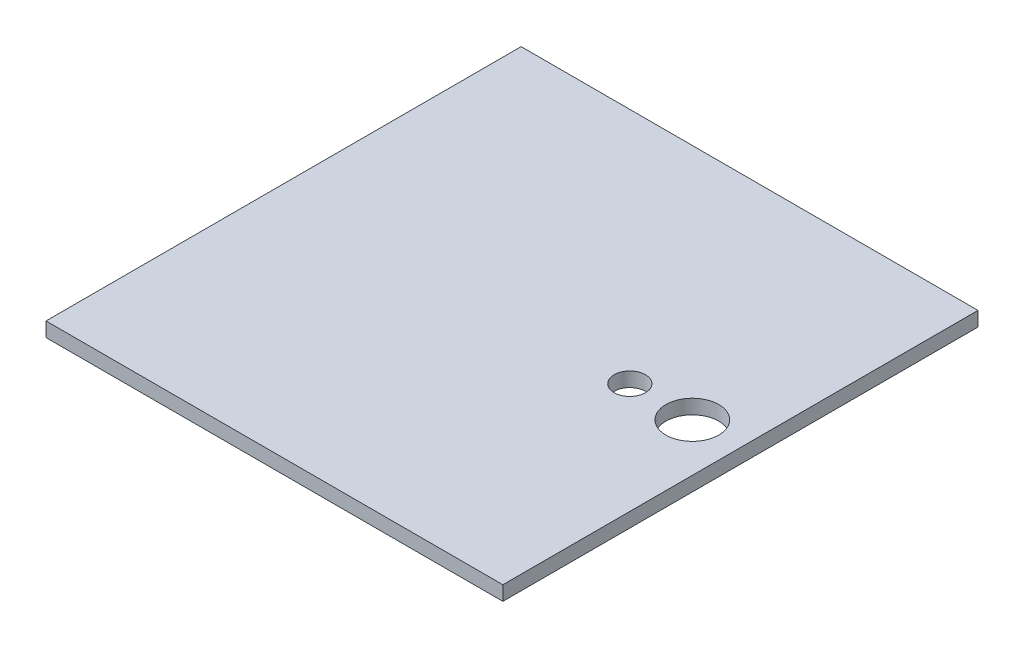
SolidWorks part; units mm, degrees
ref_plane "Front Plane" through (0, 0, 0) normal (0, 0, 1) x (1, 0, 0)
ref_plane "Top Plane" through (0, 0, 0) normal (0, 1, 0) x (1, 0, 0)
ref_plane "Right Plane" through (0, 0, 0) normal (1, 0, 0) x (0, 0, -1)
sketch "Sketch1" plane through (0, 0, 0) normal (0, 1, 0) x (1, 0, 0)
  line L1 (-101.2815, 20.698) -> (-6.2815, 20.698)
  line L2 (-101.2815, 20.698) -> (-101.2815, -78.102)
  line L3 (-101.2815, -78.102) -> (-6.2815, -78.102)
  line L4 (-6.2815, 20.698) -> (-6.2815, -78.102)
  circle A0 centre (-16.2815, -28.702) radius 5.5
  circle A1 centre (-29.2815, -28.702) radius 3.25
  point P8 (0, 0)
  dimension "D3" = 11
  dimension "D4" = 6.5
  dimension "D1" = 95
  dimension "D2" = 98.8
  dimension "D5" = 49.4
  dimension "D6" = 10
  dimension "D7" = 23
extrude "Boss-Extrude1" add sketch "Sketch1" along normal blind 3
equation "\"Fit\"= 1"
equation "\"cover width\"= 98.8"
equation "\"top 1 length\"= 95"
equation "\"thinner acrylic\"= 3"
equation "\"D1@Sketch1\"=\"top 1 length\""
equation "\"D2@Sketch1\"=\"cover width\""
equation "\"D1@Boss-Extrude1\"=\"thinner acrylic\""
equation "\"Power hole diamter\"= 11"
equation "\"D3@Sketch1\"=\"Power hole diamter\""
equation "\"switch diameter\"=6.5"
equation "\"D4@Sketch1\"=\"switch diameter\""
equation "\"D5@Sketch1\"=\"cover width\"/2"
equation "\"power hole from bottom\" = 10"
equation "\"switch hole from bottom\" = 23"
equation "\"D6@Sketch1\"=\"power hole from bottom\""
equation "\"D7@Sketch1\"=\"switch hole from bottom\""
